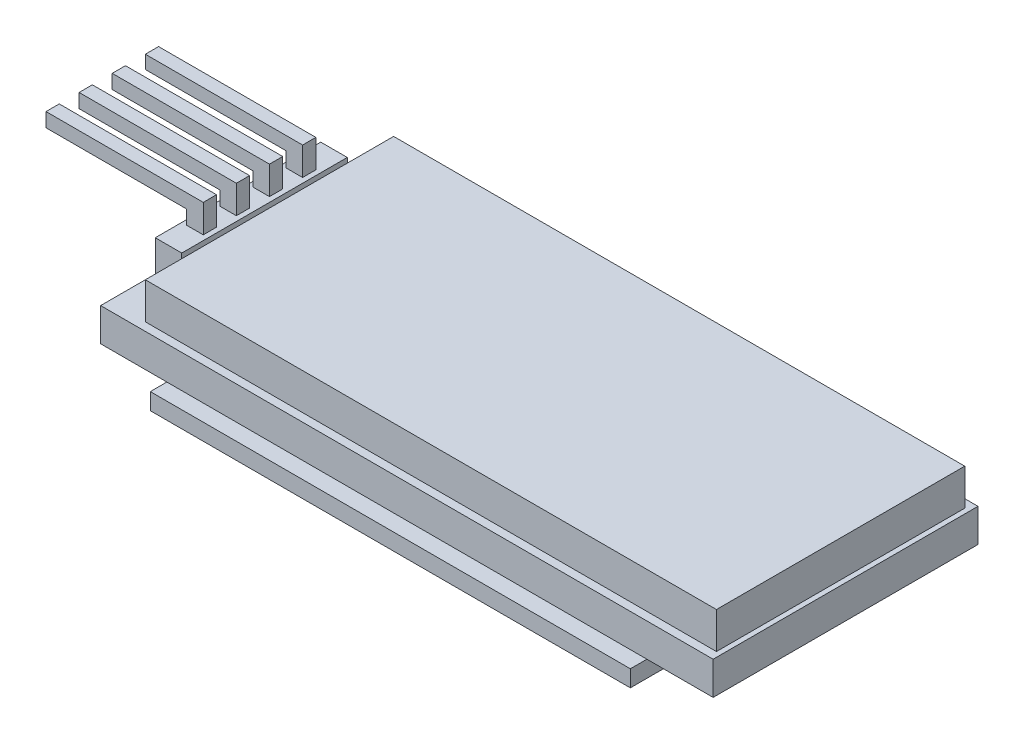
SolidWorks part; units mm, degrees
ref_plane "Front Plane" through (0, 0, 0) normal (0, 0, 1) x (1, 0, 0)
ref_plane "Top Plane" through (0, 0, 0) normal (0, 1, 0) x (1, 0, 0)
ref_plane "Right Plane" through (0, 0, 0) normal (1, 0, 0) x (0, 0, -1)
sketch "Sketch1" plane through (0, 0, 0) normal (0, 1, 0) x (1, 0, 0)
  line L1 (0, 0) -> (37, 0)
  line L2 (0, 0) -> (0, 16)
  line L3 (0, 16) -> (37, 16)
  line L4 (37, 0) -> (37, 16)
  dimension "D1" = 37
  dimension "D2" = 16
extrude "Boss-Extrude1" add sketch "Sketch1" along normal blind 2
sketch "Sketch2" plane through (0, 2, 0) normal (0, 1, 0) x (1, 0, 0)
  line L0 (37, 0) -> (37, 16) construction
  line L1 (2.2, 15.5) -> (36.7, 15.5)
  line L2 (2.2, 15.5) -> (2.2, 0.5)
  line L3 (2.2, 0.5) -> (36.7, 0.5)
  line L4 (36.7, 15.5) -> (36.7, 0.5)
  line L5 (0, 0) -> (37, 0) construction
  line L6 (0, 16) -> (0, 0) construction
  dimension "D1" = 0.3
  dimension "D2" = 15
  dimension "D3" = 0.5
  dimension "D4" = 2.2
extrude "Boss-Extrude2" add sketch "Sketch2" along normal blind 2.2
sketch "Sketch3" plane through (0, 2, 0) normal (0, 1, 0) x (1, 0, 0)
  line L0 (37, 16) -> (0, 16) construction
  line L1 (0.3, 13) -> (1.9, 13)
  line L2 (0.3, 13) -> (0.3, 3)
  line L3 (0.3, 3) -> (1.9, 3)
  line L4 (1.9, 13) -> (1.9, 3)
  line L5 (0, 16) -> (0, 0) construction
  dimension "D1" = 10
  dimension "D2" = 3
  dimension "D3" = 0.3
  dimension "D4" = 1.6
extrude "Boss-Extrude3" add sketch "Sketch3" along normal blind 2.2
sketch "Sketch4" plane through (0, 4.2, 0) normal (0, 1, 0) x (1, 0, 0)
  line L0 (0.3, 13) -> (0.3, 3) construction
  line L1 (0.6, 10.6) -> (1.6, 10.6)
  line L2 (0.6, 10.6) -> (0.6, 11.4)
  line L3 (0.6, 11.4) -> (1.6, 11.4)
  line L4 (1.6, 10.6) -> (1.6, 11.4)
  line L9 (1.9, 13) -> (0.3, 13) construction
  line L10 (0.6, 9.4) -> (1.6, 9.4)
  line L11 (1.6, 8.6) -> (1.6, 9.4)
  line L12 (0.6, 8.6) -> (0.6, 9.4)
  line L13 (0.6, 8.6) -> (1.6, 8.6)
  line L14 (0.6, 7.4) -> (1.6, 7.4)
  line L15 (1.6, 6.6) -> (1.6, 7.4)
  line L16 (0.6, 6.6) -> (0.6, 7.4)
  line L17 (0.6, 6.6) -> (1.6, 6.6)
  line L18 (0.6, 5.4) -> (1.6, 5.4)
  line L19 (1.6, 4.6) -> (1.6, 5.4)
  line L20 (0.6, 4.6) -> (0.6, 5.4)
  line L21 (0.6, 4.6) -> (1.6, 4.6)
  dimension "D1" = 1
  dimension "D2" = 0.3
  dimension "D3" = 1.6
  dimension "D4" = 0.8
  dimension "D5" = 4
extrude "Boss-Extrude4" add sketch "Sketch4" along normal blind 1.7 and the other way blind 6
sketch "Sketch5" plane through (0.6, 0, 0) normal (-1, 0, 0) x (0, 0, 1)
  line L0 (-10.6, 5.9) -> (-10.6, 4.2) construction
  line L1 (-11.4, 5.9) -> (-10.6, 5.9)
  line L2 (-11.4, 5.9) -> (-11.4, 5.1)
  line L3 (-11.4, 5.1) -> (-10.6, 5.1)
  line L4 (-10.6, 5.9) -> (-10.6, 5.1)
  line L5 (-8.6, 5.9) -> (-8.6, 4.2) construction
  line L6 (-9.4, 5.9) -> (-8.6, 5.9)
  line L7 (-9.4, 5.9) -> (-9.4, 5.05)
  line L8 (-9.4, 5.05) -> (-8.6, 5.05)
  line L9 (-8.6, 5.9) -> (-8.6, 5.05)
  line L10 (-6.6, 5.9) -> (-6.6, 4.2) construction
  line L11 (-7.4, 5.9) -> (-6.6, 5.9)
  line L12 (-7.4, 5.9) -> (-7.4, 5.05)
  line L13 (-7.4, 5.05) -> (-6.6, 5.05)
  line L14 (-6.6, 5.9) -> (-6.6, 5.05)
  line L15 (-4.6, 5.9) -> (-4.6, 4.2) construction
  line L16 (-5.4, 5.9) -> (-4.6, 5.9)
  line L17 (-5.4, 5.9) -> (-5.4, 5.05)
  line L18 (-5.4, 5.05) -> (-4.6, 5.05)
  line L19 (-4.6, 5.9) -> (-4.6, 5.05)
  dimension "D1" = 0.8
extrude "Boss-Extrude5" add sketch "Sketch5" along normal blind 8.5
sketch "Sketch6" plane through (0, 0, 0) normal (0, -1, 0) x (-1, 0, 0)
  line L0 (-37, 0) -> (-37, 16) construction
  line L1 (-4, -1) -> (-33, -1)
  line L2 (-4, -1) -> (-4, 17)
  line L3 (-4, 17) -> (-33, 17)
  line L4 (-33, -1) -> (-33, 17)
  line L5 (0, 0) -> (-37, 0) construction
  dimension "D1" = 29
  dimension "D2" = 4
  dimension "D3" = 18
  dimension "D4" = 1
extrude "Boss-Extrude6" add sketch "Sketch6" along normal blind 1
